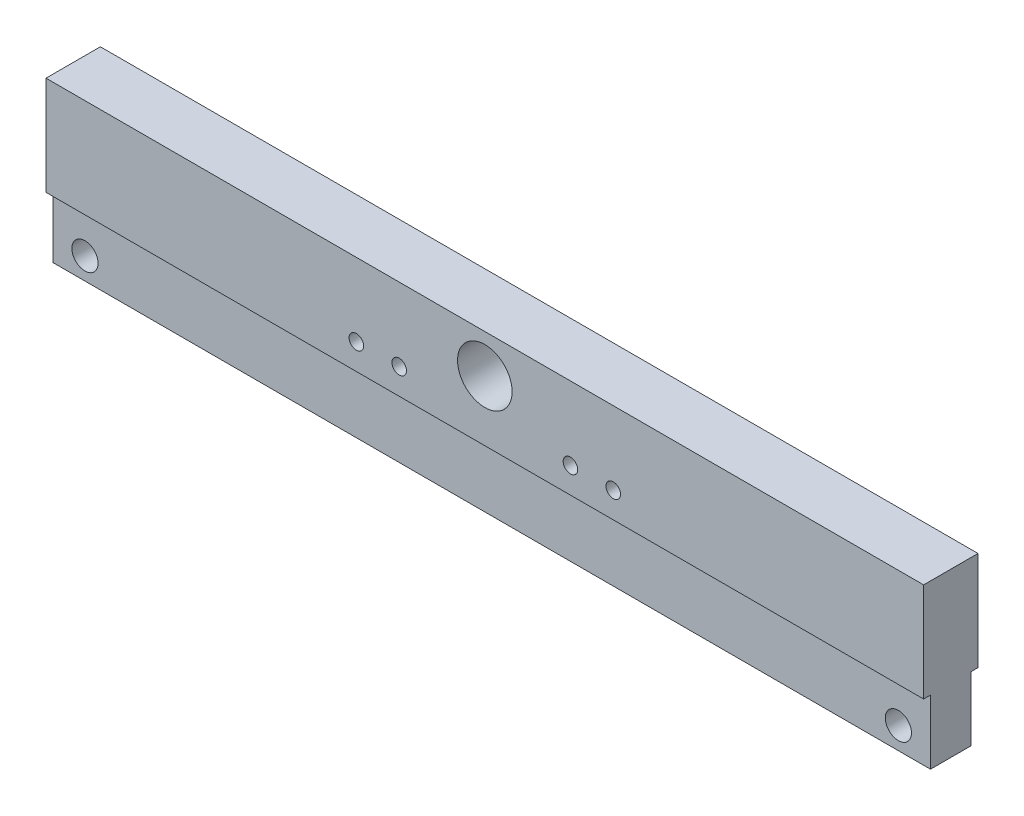
SolidWorks part; units mm, degrees
ref_plane "Front Plane" through (0, 0, 0) normal (0, 0, 1) x (1, 0, 0)
ref_plane "Top Plane" through (0, 0, 0) normal (0, 1, 0) x (1, 0, 0)
ref_plane "Right Plane" through (0, 0, 0) normal (1, 0, 0) x (0, 0, -1)
sketch "Sketch1" plane through (0, 0, 0) normal (0, 0, 1) x (1, 0, 0)
  line L0 (0, 0) -> (0, 68.885) construction
  line L1 (0, 0) -> (54, 0) construction
  line L3 (-205, 38.1) -> (205, 38.1)
  line L4 (-205, 38.1) -> (-205, -38.1)
  line L5 (-205, -38.1) -> (205, -38.1)
  line L6 (205, 38.1) -> (205, -38.1)
  circle A0 centre (0, 20.1) radius 12.75
  circle A1 centre (190, -27.9) radius 6.125
  circle A2 centre (-190, -27.9) radius 6.125
  dimension "D3" = 12.25
  dimension "D7" = 25.5
  dimension "D1" = 410
  dimension "D2" = 76.2
  dimension "D4" = 380
  dimension "D5" = 48
  dimension "D6" = 18
extrude "Boss-Extrude1" add sketch "Sketch1" along normal mid plane 25.4
sketch "Sketch2" plane through (0, -38.1, 0) normal (0, -1, 0) x (1, 0, 0)
  line L0 (0, -12.7) -> (0, 12.7) construction
  line L1 (-205, 12.7) -> (205, 12.7) construction
  line L2 (0, 0) -> (-165, 0) construction
  line L3 (-205, -12.7) -> (205, -12.7) construction
  circle A0 centre (0, 0) radius 6
  circle A1 centre (-165, 0) radius 6
  circle A2 centre (165, 0) radius 6
  point P11 (0, 0)
  point P12 (0, -9.525)
  dimension "D1" = 12
  dimension "D2" = 165
extrude "Cut-Extrude1" cut sketch "Sketch2" against normal blind 15
sketch "Sketch4" plane through (0, -38.1, 0) normal (0, -1, 0) x (1, 0, 0)
  line L0 (-205, 12.7) -> (-205, -12.7) construction
  line L1 (205, -9.5) -> (-205, -9.5)
  line L2 (205, -9.5) -> (205, 9.5)
  line L3 (205, 9.5) -> (-205, 9.5)
  line L4 (-205, -9.5) -> (-205, 9.5)
  line L5 (205, -9.5) -> (-205, 9.5) construction
  line L6 (205, 9.5) -> (-205, -9.5) construction
  point P0 (0, 0)
  dimension "D1" = 19
extrude "Cut-Extrude2" cut sketch "Sketch4" against normal blind 30 flip side to cut
hole_wizard "M8 Tapped Hole1" positions "Sketch5" profile "Sketch7" tap size "M8" standard "ISO" end condition through all
sketch "Sketch5" plane through (0, 0, 12.7) normal (0, 0, 1) x (1, 0, 0)
  line L0 (0, 0) -> (0, 71.8268) construction
  line L3 (-205, -8.1) -> (205, -8.1) construction
  point P0 (-60, 3.9)
  point P2 (-40, 3.9)
  point P15 (0, 0)
  point P16 (40, 3.9)
  point P17 (60, 3.9)
  dimension "D1" = 12
  dimension "D2" = 80
  dimension "D3" = 20
sketch "Sketch7" plane through (-60, 3.9, 12.7) normal (1, 0, 0) x (0, -1, 0)
  line L0 (0, 0) -> (0, 25.4)
  line L1 (0, 25.4) -> (3.4, 25.4)
  line L2 (3.4, 25.4) -> (3.4, 0)
  line L5 (3.4, 0) -> (0, 0)
  line L11 (0, -6.35) -> (0, 107.95) construction
  dimension "Thru Tap Drill Dia." = 6.8
  dimension "Thru Tap Drill Depth" = 25.4
cosmetic thread "Hole Thread1" parameters "D2"=8
cosmetic thread "Hole Thread2" parameters "D2"=8
cosmetic thread "Hole Thread3" parameters "D2"=8
cosmetic thread "Hole Thread4" parameters "D2"=8
